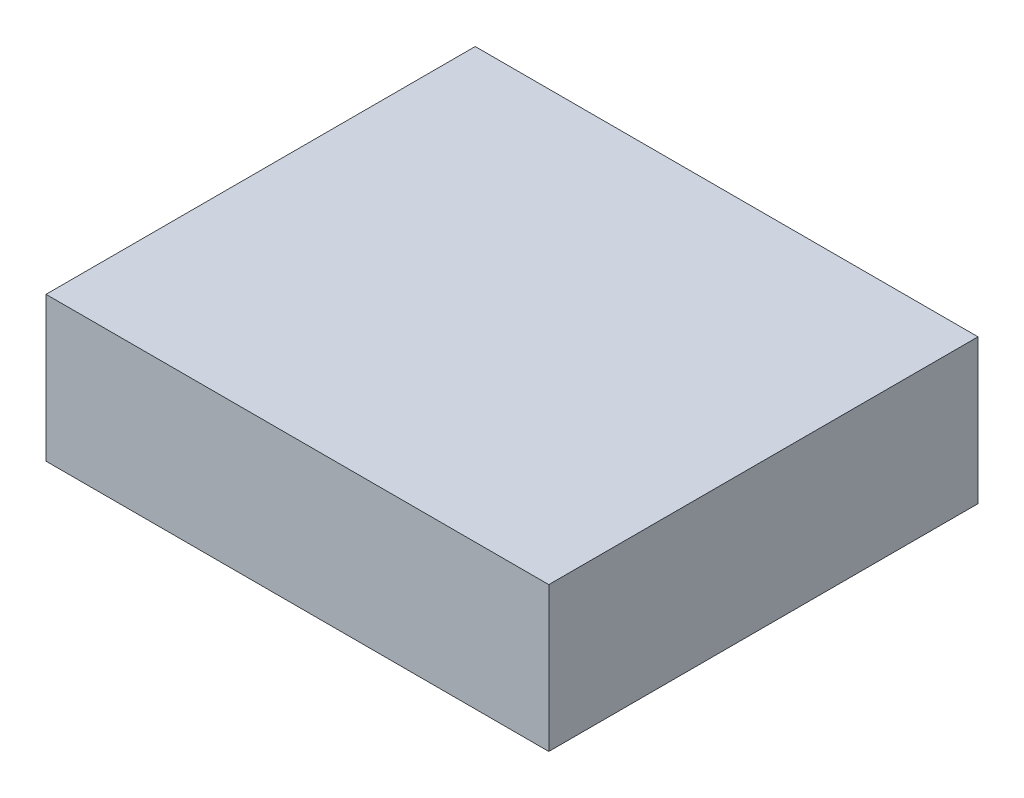
SolidWorks part; units mm, degrees
ref_plane "Front Plane" through (0, 0, 0) normal (0, 0, 1) x (1, 0, 0)
ref_plane "Top Plane" through (0, 0, 0) normal (0, 1, 0) x (1, 0, 0)
ref_plane "Right Plane" through (0, 0, 0) normal (1, 0, 0) x (0, 0, -1)
sketch "Sketch1" plane through (0, 0, 0) normal (0, 1, 0) x (1, 0, 0)
  line L0 (0, 24.5) -> (0, 0) construction
  line L1 (-28.7, 24.5) -> (28.7, 24.5)
  line L2 (-28.7, 24.5) -> (-28.7, -24.5)
  line L3 (-28.7, -24.5) -> (28.7, -24.5)
  line L4 (28.7, 24.5) -> (28.7, -24.5)
  line L5 (0, 0) -> (-28.7, 0) construction
  dimension "D1" = 57.4
  dimension "D2" = 49
extrude "Boss-Extrude1" add sketch "Sketch1" along normal blind 16.5
